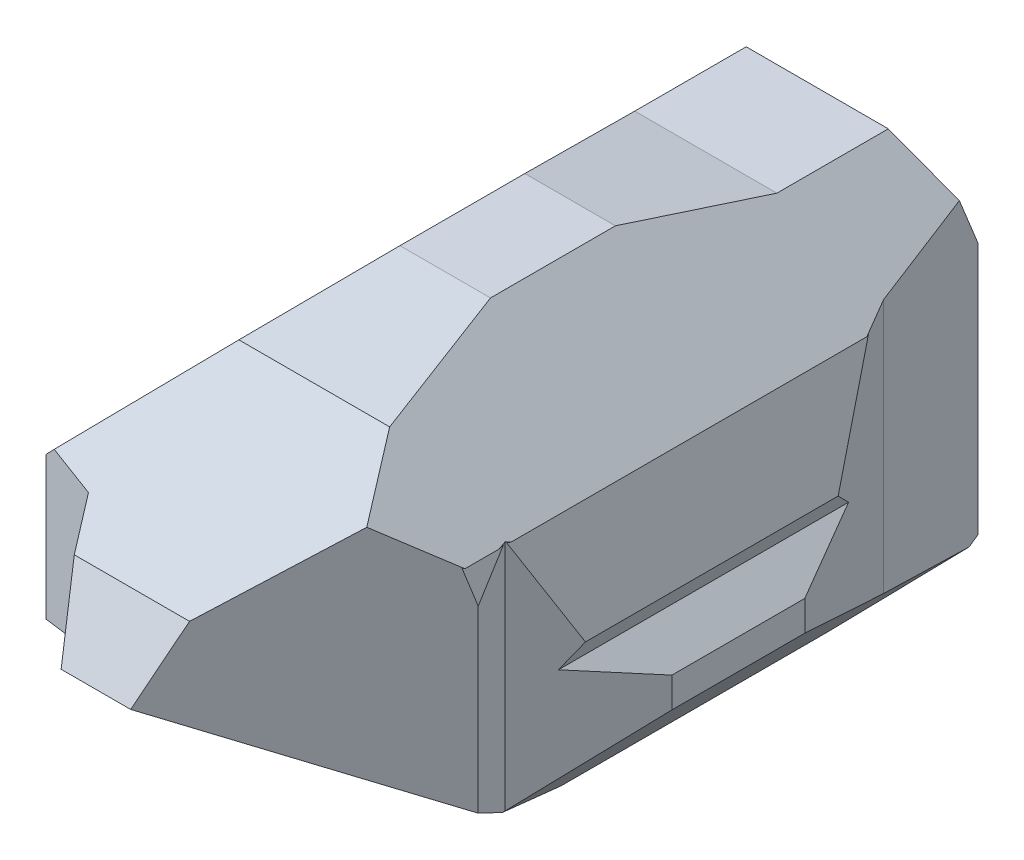
SolidWorks part; units mm, degrees
ref_plane "Plan de face" through (0, 0, 0) normal (0, 0, 1) x (1, 0, 0)
ref_plane "Plan de dessus" through (0, 0, 0) normal (0, 1, 0) x (1, 0, 0)
ref_plane "Plan de droite" through (0, 0, 0) normal (1, 0, 0) x (0, 0, -1)
sketch "Esquisse1" plane through (0, 0, 0) normal (0, 0, 1) x (1, 0, 0)
  line L1 (0, 0) -> (15, 0)
  line L2 (0, 0) -> (0, 15)
  line L3 (0, 15) -> (15, 15)
  line L4 (15, 0) -> (15, 15)
  dimension "D1" = 15
  dimension "D2" = 15
extrude "Boss.-Extru.1" add sketch "Esquisse1" along normal blind 30
sketch "Esquisse2" plane through (0, 0, 0) normal (-1, 0, 0) x (0, 0, 1)
  line L0 (30, 7.5) -> (17.1572, 0)
  line L1 (30, 15) -> (30, 0) construction
  line L2 (30, 0) -> (0, 0) construction
  line L3 (17.1572, 0) -> (30, 0)
  line L4 (30, 0) -> (30, 7.5)
extrude "Enlèv. mat.-Extru.1" cut sketch "Esquisse2" against normal blind 30
sketch "Esquisse3" plane through (0, 0, 0) normal (-1, 0, 0) x (0, 0, 1)
  line L0 (30, 7.5) -> (28.7755, 10.065)
  line L1 (28.7755, 10.065) -> (21.2277, 15)
  line L2 (30, 15) -> (0, 15) construction
  line L3 (21.2277, 15) -> (30, 15)
  line L4 (30, 15) -> (30, 7.5)
extrude "Enlèv. mat.-Extru.2" cut sketch "Esquisse3" against normal blind 30
sketch "Esquisse4" plane through (0, 0, 0) normal (-1, 0, 0) x (0, 0, 1)
  line L0 (13.8022, 15) -> (8.9263, 14.0316)
  line L1 (21.2277, 15) -> (0, 15) construction
  line L2 (8.9263, 14.0316) -> (4.9326, 14.0316)
  line L3 (4.9326, 14.0316) -> (3.2118, 10.3707)
  line L4 (3.2118, 10.3707) -> (1.6629, 6.1243)
  line L5 (1.6629, 6.1243) -> (0, 5.0691)
  line L6 (0, 15) -> (0, 0) construction
  line L7 (0, 5.0691) -> (0, 3.1484)
  line L8 (0, 3.1484) -> (3.2118, 1.3212)
  line L9 (3.2118, 1.3212) -> (7.6328, 0)
  line L10 (17.1572, 0) -> (0, 0) construction
  line L11 (7.6328, 0) -> (0, 0)
  line L12 (0, 0) -> (0, 15)
  line L13 (0, 15) -> (13.8022, 15)
  line M4 (21.2277, 15) -> (0, 15)
  line M5 (0, 15) -> (0, 0)
  line M6 (0, 0) -> (17.1572, 0)
extrude "Enlèv. mat.-Extru.3" cut sketch "Esquisse4" against normal blind 30 contours L5 L4 L3 L2 L0 M4 M5 | L9 L8 M5 M6
sketch "Esquisse5" plane through (0, -7.4715, 4.3632) normal (0, -0.8635, 0.5043) x (-1, 0, 0)
  line L0 (-5.9517, -29.6882) -> (-4.3854, -26.7395)
  line L1 (0, -29.6882) -> (-15, -29.6882) construction
  line L2 (-4.3854, -26.7395) -> (-2.3165, -26.1061)
  line L3 (-2.3165, -26.1061) -> (-0.7659, -20.31)
  line L4 (-0.7659, -20.31) -> (-2.8311, -15.9644)
  line L5 (-2.8311, -15.9644) -> (-2.5239, -14.8158)
  line L6 (-15, -14.8158) -> (0, -14.8158) construction
  line L7 (-2.5239, -14.8158) -> (0, -14.8158)
  line L8 (0, -14.8158) -> (0, -29.6882)
  line L9 (0, -29.6882) -> (0, -14.8158) construction
  line L10 (0, -29.6882) -> (-5.9517, -29.6882)
extrude "Enlèv. mat.-Extru.5" cut sketch "Esquisse5" along direction (0, -1, 0) on the side against the normal blind 30
sketch "Esquisse6" plane through (0, 0, 0) normal (0, -1, 0) x (-1, 0, 0)
  line L0 (-2.5239, -17.1572) -> (-0.6191, -13.9578)
  line L1 (-0.6191, -13.9578) -> (-1.0648, -9.6148)
  line L2 (-1.0648, -9.6148) -> (-2.2254, -6.0936)
  line L3 (-2.2254, -6.0936) -> (-2.6786, -1.6771)
  line L4 (-2.6786, -1.6771) -> (-4.8338, 0.9709)
  line L5 (-4.8338, 0.9709) -> (-8.6983, 0)
  line L6 (-8.6983, 0) -> (-11.6098, -2.3696)
  line L7 (-11.6098, -2.3696) -> (-13.4587, -7.2462)
  line L8 (-13.4587, -7.2462) -> (-15, -9.8352)
  line L9 (-15, -17.1572) -> (-15, -7.6328) construction
  line L10 (-15, -9.8352) -> (-14.3698, -12.3435)
  line L11 (-14.3698, -12.3435) -> (-15, -14.0056)
  line L12 (-15, -14.0056) -> (-14.3698, -16.5139)
  line L13 (-14.3698, -16.5139) -> (-14.6849, -18.5673)
  line L14 (-14.6849, -18.5673) -> (-12.1236, -22.8274)
  line L15 (-12.1236, -22.8274) -> (-13.4042, -26.2052)
  line L16 (-13.4042, -26.2052) -> (-11.4553, -28.5999)
  line L17 (-11.4553, -28.5999) -> (-9.361, -28.9213)
  line L18 (-9.361, -28.9213) -> (-15.4731, -28.9213)
  line L19 (-15.4731, -28.9213) -> (-14.2294, 0.9709)
  line L20 (-14.2294, 0.9709) -> (-4.8338, 0.9709)
  line L21 (0.575, 0.9709) -> (0, -17.1572)
  line L22 (0, -17.1572) -> (-2.5239, -17.1572)
  line M24 (0, -7.6328) -> (-15, -7.6328)
  line M27 (-2.5239, -17.1572) -> (0, -17.1572)
  line M28 (0, -17.1572) -> (0, -7.6328)
extrude "Enlèv. mat.-Extru.7" cut sketch "Esquisse6" against normal blind 30 contours L2 L1 L0 M27 M28 M24
sketch "Esquisse8" plane through (0, 2.094, 0.6258) normal (0, -0.9581, -0.2863) x (1, 0, 0)
  line L0 (1.7181, 7.3132) -> (0.6286, 4.8583)
  line L1 (0.6286, 4.8583) -> (1.4605, 2.699)
  line L2 (15, 2.699) -> (0, 2.699) construction
  line L3 (1.4605, 2.699) -> (0, 2.699)
  line L4 (0, 2.699) -> (0, 7.3132)
  line L5 (0, 7.3132) -> (1.7181, 7.3132)
extrude "Enlèv. mat.-Extru.8" cut sketch "Esquisse8" along direction (0, -1, 0) on the side against the normal blind 30
sketch "Esquisse9" plane through (0, 2.3786, 1.3532) normal (0, -0.8692, -0.4945) x (1, 0, 0)
  line L0 (1.4605, 2.1383) -> (3.3434, -0.7974)
  line L1 (3.3434, -0.7974) -> (4.7469, -1.5568)
  line L2 (15, -1.5568) -> (0, -1.5568) construction
  line L3 (4.7469, -1.5568) -> (7.1145, -1.5568)
  line L4 (7.1145, -1.5568) -> (9.7416, -1.1771)
  line L5 (9.7416, -1.1771) -> (12.941, -0.7147)
  line L6 (12.941, -0.7147) -> (14.5066, 0.9432)
  line L7 (14.5066, 0.9432) -> (15, 2.1383)
  line L8 (15, 2.1383) -> (15, -1.5568)
  line L9 (15, -1.5568) -> (0, -1.5568)
  line L10 (0, -1.5568) -> (0, 2.1383)
  line L11 (0, 2.1383) -> (1.4605, 2.1383)
  line M1 (15, -1.5568) -> (15, 2.1383)
  line M3 (1.4605, 2.1383) -> (0, 2.1383)
  line M4 (0, 2.1383) -> (0, -1.5568)
  line M5 (0, -1.5568) -> (15, -1.5568)
extrude "Enlèv. mat.-Extru.13" cut sketch "Esquisse9" along direction (0, 1, 0) on the side against the normal blind 30 contours L7 L6 L5 L4 M5 M1 | L1 L0 M3 M4 M5
sketch "Esquisse12" plane through (0, -7.4715, 4.3632) normal (0, -0.8635, 0.5043) x (-1, 0, 0)
  line L0 (-9.6735, -29.6882) -> (-12.6501, -26.7115)
  line L1 (-5.9517, -29.6882) -> (-15, -29.6882) construction
  line L2 (-12.6501, -26.7115) -> (-14.1799, -24.1059)
  line L3 (-14.1799, -24.1059) -> (-13.415, -19.9036)
  line L4 (-13.415, -19.9036) -> (-15, -14.8158)
  line L5 (-15, -14.8158) -> (-15, -29.6882)
  line L6 (-15, -29.6882) -> (-9.6735, -29.6882)
extrude "Enlèv. mat.-Extru.15" cut sketch "Esquisse12" along direction (0, -1, 0) on the side against the normal blind 30
sketch "Esquisse13" plane through (0, 0, 0) normal (0, -1, 0) x (-1, 0, 0)
  line L0 (-15, -12.395) -> (-13.0603, -7.6328)
  line L1 (-15, -17.1572) -> (-15, -7.6328) construction
  line L2 (-15, -7.6328) -> (-1.7181, -7.6328) construction
  line L3 (-13.0603, -7.6328) -> (-15, -7.6328)
  line L4 (-15, -7.6328) -> (-15, -12.395)
extrude "Enlèv. mat.-Extru.16" cut sketch "Esquisse13" against normal blind 30
sketch "Esquisse14" plane through (0, 2.094, 0.6258) normal (0, -0.9581, -0.2863) x (1, 0, 0)
  line L0 (13.0603, 7.3132) -> (12.0245, 2.699)
  line L1 (15, 2.699) -> (1.4605, 2.699) construction
  line L2 (12.0245, 2.699) -> (15, 2.699)
  line L3 (15, 2.699) -> (15, 7.3132)
  line L4 (15, 7.3132) -> (13.0603, 7.3132)
extrude "Enlèv. mat.-Extru.17" cut sketch "Esquisse14" along direction (0, 1, 0) on the side against the normal blind 30
sketch "Esquisse15" plane through (0, 2.3786, 1.3532) normal (0, -0.8692, -0.4945) x (-1, 0, 0)
  line L0 (-12.0245, -2.1383) -> (-8.5346, 1.3516)
  line L1 (-7.1145, 1.5568) -> (-12.941, 0.7147) construction
  line L2 (-8.5346, 1.3516) -> (-12.941, 0.7147)
  line L3 (-12.941, 0.7147) -> (-14.5066, -0.9432)
  line L4 (-14.5066, -0.9432) -> (-15, -2.1383)
  line L5 (-15, -2.1383) -> (-12.0245, -2.1383)
extrude "Enlèv. mat.-Extru.18" cut sketch "Esquisse15" along direction (0, 1, 0) on the side against the normal blind 30
sketch "Esquisse16" plane through (0, 0, 0) normal (0, 0, -1) x (-1, 0, 0)
  line L0 (-15.3961, 8.8612) -> (-9.1239, 15.5269)
  line L1 (-9.1239, 15.5269) -> (-16.1831, 15.5269)
  line L2 (-16.1831, 15.5269) -> (-15.3961, 8.8612)
extrude "Enlèv. mat.-Extru.19" cut sketch "Esquisse16" against normal blind 30
sketch "Esquisse17" plane through (0, 0, 0) normal (0, 0, -1) x (-1, 0, 0)
  line L0 (-6.5542, 15.1865) -> (0.6692, 7.7161)
  line L1 (0.6692, 7.7161) -> (0.6692, 16.0714)
  line L2 (0.6692, 16.0714) -> (-6.5542, 15.1865)
extrude "Enlèv. mat.-Extru.20" cut sketch "Esquisse17" against normal blind 30
sketch "Esquisse18" plane through (0, 0, 0) normal (0, 0, -1) x (-1, 0, 0)
  line L0 (-15, 9.2184) -> (-13.9217, 6.5431)
  line L1 (-15, 9.2821) -> (-15, 0) construction
  line L2 (-13.9217, 6.5431) -> (-15.5063, 4.8967)
  line L3 (-15.5063, 4.8967) -> (-10.238, -0.8656)
  line L4 (-10.238, -0.8656) -> (-16.3872, -0.5902)
  line L5 (-16.3872, -0.5902) -> (-18.5521, 8.7039)
  line L6 (-18.5521, 8.7039) -> (-15.8781, 10.7797)
  line L7 (-15.8781, 10.7797) -> (-15, 9.2184)
extrude "Enlèv. mat.-Extru.21" cut sketch "Esquisse18" against normal blind 30
sketch "Esquisse19" plane through (0, 0, 0) normal (0, 0, -1) x (-1, 0, 0)
  line L0 (-5.8751, -0.7215) -> (0.1753, 5.617)
  line L1 (0.1753, 5.617) -> (0.8544, -0.5775)
  line L2 (0.8544, -0.5775) -> (-3.5084, -1.483)
  line L3 (-3.5084, -1.483) -> (-5.8751, -0.7215)
extrude "Enlèv. mat.-Extru.22" cut sketch "Esquisse19" against normal blind 30
sketch "Esquisse20" plane through (0, 0, 0) normal (0, -1, 0) x (1, 0, 0)
  line L0 (14.6415, 21.4316) -> (7.4164, 31.4207)
  line L1 (7.4164, 31.4207) -> (22.8215, 29.7007)
  line L2 (22.8215, 29.7007) -> (19.1934, 23.5264)
  line L3 (19.1934, 23.5264) -> (14.6415, 21.4316)
extrude "Enlèv. mat.-Extru.23" cut sketch "Esquisse20" against normal blind 30
sketch "Esquisse21" plane through (15, 0, 0) normal (1, 0, 0) x (0, 0, -1)
  line L0 (-25.2515, 13.3143) -> (-17.635, 15.1558)
  line L1 (-17.635, 15.1558) -> (-22.6504, 16.3081)
  line L2 (-22.6504, 16.3081) -> (-25.7917, 15.5486)
  line L3 (-25.7917, 15.5486) -> (-25.2515, 13.3143)
  point P2 (-17.635, 15.1558)
extrude "Enlèv. mat.-Extru.25" cut sketch "Esquisse21" against normal blind 30
sketch "Esquisse22" plane through (0, 0, 0) normal (0, 0, -1) x (-1, 0, 0)
  line L0 (-14.1785, 7.1806) -> (-13.4302, 10.9187)
  line L1 (-13.4302, 10.9187) -> (-15.8929, 10.1343)
  line L2 (-15.8929, 10.1343) -> (-16.3589, 7.806)
  line L3 (-16.3589, 7.806) -> (-14.1785, 7.1806)
extrude "Enlèv. mat.-Extru.26" cut sketch "Esquisse22" against normal blind 30
